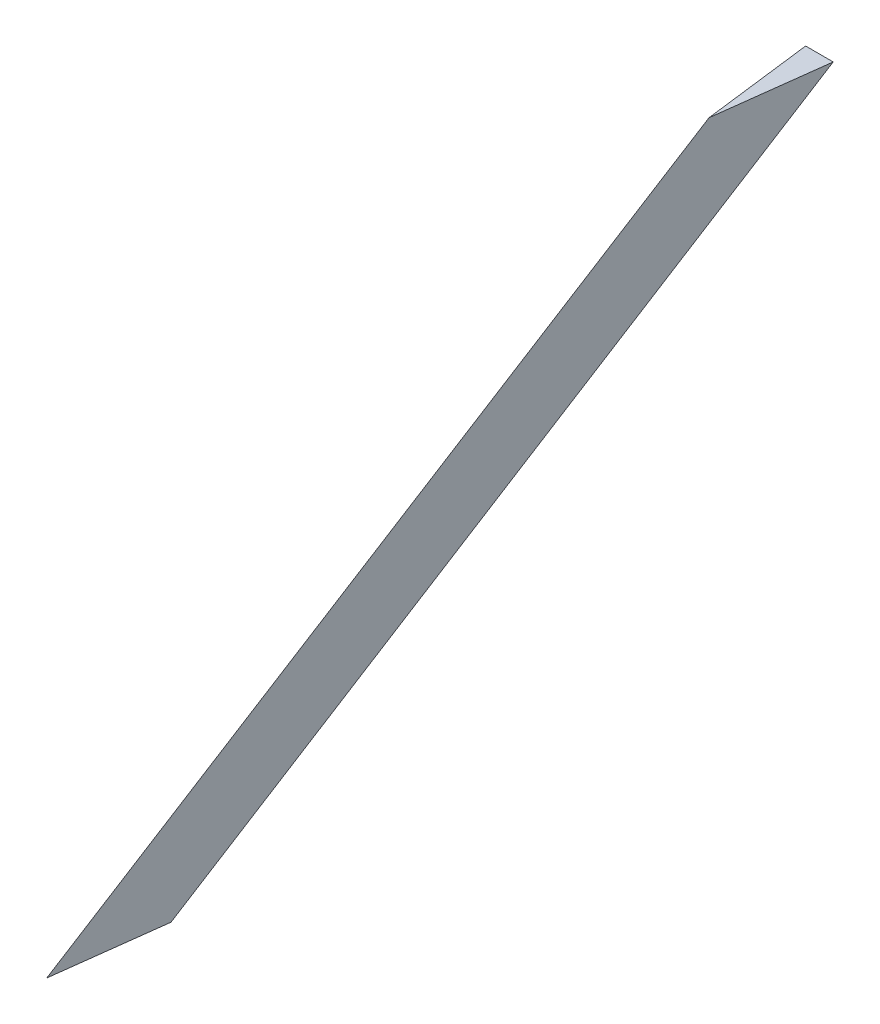
SolidWorks part; units mm, degrees
material "E-Glass Fiber"
ref_plane "Front Plane" through (0, 0, 0) normal (0, 0, 1) x (1, 0, 0)
ref_plane "Top Plane" through (0, 0, 0) normal (0, 1, 0) x (1, 0, 0)
ref_plane "Right Plane" through (0, 0, 0) normal (1, 0, 0) x (0, 0, -1)
sketch "Sketch1" plane through (0, 0, 0) normal (1, 0, 0) x (0, 0, -1)
  line L0 (0, 0) -> (152.4, 95.25)
  dimension "D1" = 152.4
  dimension "D2" = 95.25
sketch "Sketch2" plane through (0, 0, 0) normal (0, 1, 0) x (1, 0, 0)
  line L1 (0, -25.4) -> (-3.175, 0)
  line L2 (-3.175, 0) -> (3.175, 0)
  line L3 (3.175, 0) -> (0, -25.4)
  dimension "D1" = 6.35
  dimension "D2" = 25.4
sweep "Sweep1" add profiles "Sketch2" path "Sketch1"
